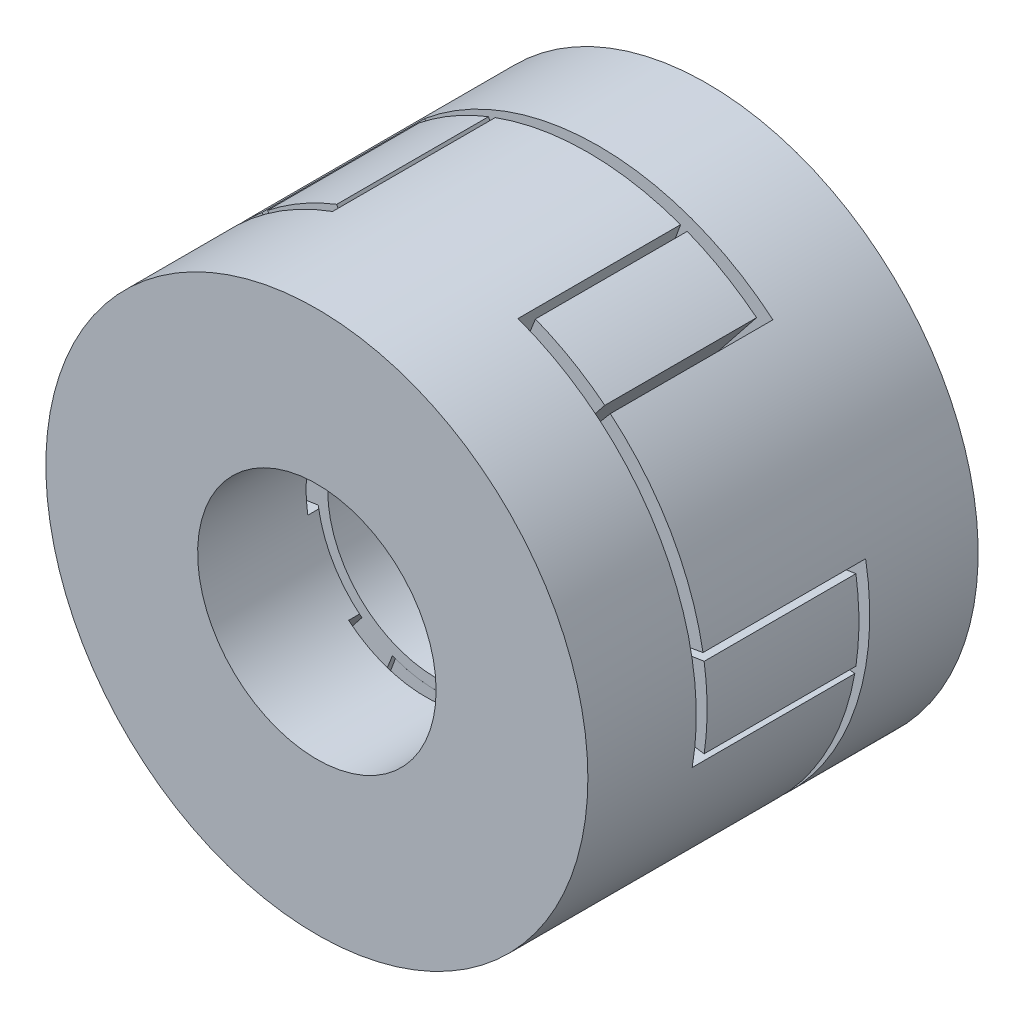
SolidWorks part; units mm, degrees
ref_plane "前视基准面" through (0, 0, 0) normal (0, 0, 1) x (1, 0, 0)
ref_plane "上视基准面" through (0, 0, 0) normal (0, 1, 0) x (1, 0, 0)
ref_plane "右视基准面" through (0, 0, 0) normal (1, 0, 0) x (0, 0, -1)
other "Configuration Table"
sketch "草图1" plane through (0, 0, 0) normal (0, 0, 1) x (1, 0, 0)
  circle A0 centre (0, 0) radius 25
  circle A1 centre (0, 0) radius 11
  dimension "D1" = 50
  dimension "D2" = 22
extrude "凸台-拉伸1" add sketch "草图1" along normal blind 25
sketch "草图2" plane through (0, 0, 0) normal (0, 0, -1) x (-1, 0, 0)
  line L0 (0, 0) -> (-20.9775, -25)
  line L1 (-20.9775, -25) -> (20.9775, -25)
  line L2 (20.9775, -25) -> (0, 0)
  line L3 (0, 0) -> (0, -25) construction
  line L4 (-32.1394, -5.667) -> (0, 0)
  line L5 (0, 0) -> (-11.1619, 30.667)
  line L6 (-11.1619, 30.667) -> (-32.1394, -5.667)
  line L7 (11.1619, 30.667) -> (0, 0)
  line L8 (0, 0) -> (32.1394, -5.667)
  line L9 (32.1394, -5.667) -> (11.1619, 30.667)
  circle A0 centre (0, 0) radius 25 construction
  point P14 (0, 0)
  circle M5 centre (0, 0) radius 25
  circle M6 centre (0, 0) radius 11
  dimension "D1" = 80
  dimension "D2" = 3
extrude "切除-拉伸1" cut sketch "草图2" against normal blind 15 contours L5 L4 M6 M5 | L8 L7 M6 M5 | L3 L0 M6 M5 | L3 L2 M6 M5
ref_plane "基准面1" through (0, 0, 14) normal (0, 0, -1) x (-1, 0, 0)
sketch "草图3" plane through (0, 0, 14) normal (0, 0, -1) x (-1, 0, 0)
  circle A0 centre (0, 0) radius 25
  circle A1 centre (0, 0) radius 11
  dimension "D1" = 50
  dimension "D2" = 22
extrude "凸台-拉伸3" add sketch "草图3" along normal blind 25 separate body
sketch "草图4" plane through (0, 0, 14) normal (0, 0, 1) x (1, 0, 0)
  line L0 (0, 0) -> (20.9775, 25)
  line L1 (20.9775, 25) -> (-20.9775, 25)
  line L2 (-20.9775, 25) -> (0, 0)
  line L3 (0, 0) -> (0, 25) construction
  line L4 (32.1394, 5.667) -> (0, 0)
  line L5 (0, 0) -> (11.1619, -30.667)
  line L6 (11.1619, -30.667) -> (32.1394, 5.667)
  line L7 (-11.1619, -30.667) -> (0, 0)
  line L8 (0, 0) -> (-32.1394, 5.667)
  line L9 (-32.1394, 5.667) -> (-11.1619, -30.667)
  circle A0 centre (0, 0) radius 25 construction
  point P13 (0, 0)
  circle M5 centre (0, 0) radius 25
  circle M6 centre (0, 0) radius 11
  dimension "D1" = 80
  dimension "D2" = 3
extrude "切除-拉伸2" cut sketch "草图4" against normal blind 15 contours L3 L2 M6 M5 | L3 L0 M6 M5 | L5 L4 M6 M5 | L8 L7 M6 M5
sketch "草图5" plane through (0, 0, 14) normal (0, 0, -1) x (-1, 0, 0)
  circle A0 centre (0, 0) radius 25
  circle A1 centre (0, 0) radius 10
  dimension "D1" = 50
  dimension "D2" = 20
extrude "凸台-拉伸5" add sketch "草图5" along normal blind 14 separate body
sketch "草图6" plane through (0, 0, 0) normal (0, 0, -1) x (-1, 0, 0)
  line L0 (0, 0) -> (9.8478, 25)
  line L1 (9.8478, 25) -> (-9.8478, 25)
  line L2 (-9.8478, 25) -> (0, 0)
  line L3 (0, 0) -> (0, 25) construction
  line L4 (16.7268, 21.0284) -> (0, 0)
  line L5 (0, 0) -> (26.5745, 3.9716)
  line L6 (26.5745, 3.9716) -> (16.7268, 21.0284)
  line L7 (26.5745, -3.9716) -> (0, 0)
  line L8 (0, 0) -> (16.7268, -21.0284)
  line L9 (16.7268, -21.0284) -> (26.5745, -3.9716)
  line L10 (9.8478, -25) -> (0, 0)
  line L11 (0, 0) -> (-9.8478, -25)
  line L12 (-9.8478, -25) -> (9.8478, -25)
  line L13 (-16.7268, -21.0284) -> (0, 0)
  line L14 (0, 0) -> (-26.5745, -3.9716)
  line L15 (-26.5745, -3.9716) -> (-16.7268, -21.0284)
  line L16 (-26.5745, 3.9716) -> (0, 0)
  line L17 (0, 0) -> (-16.7268, 21.0284)
  line L18 (-16.7268, 21.0284) -> (-26.5745, 3.9716)
  circle A0 centre (0, 0) radius 25 construction
  circle A1 centre (0, 0) radius 11
  point P20 (0, 0)
  circle M5 centre (0, 0) radius 25
  dimension "D3" = 22
  dimension "D1" = 43
  dimension "D2" = 6
extrude "切除-拉伸5" cut sketch "草图6" against normal blind 14 contours A1 L17 L16 M5 | A1 L3 L2 M5 | L3 A1 L0 M5 | A1 L5 L4 M5 | A1 L8 L7 M5 | A1 L11 L10 M5 | A1 L14 L13 M5
